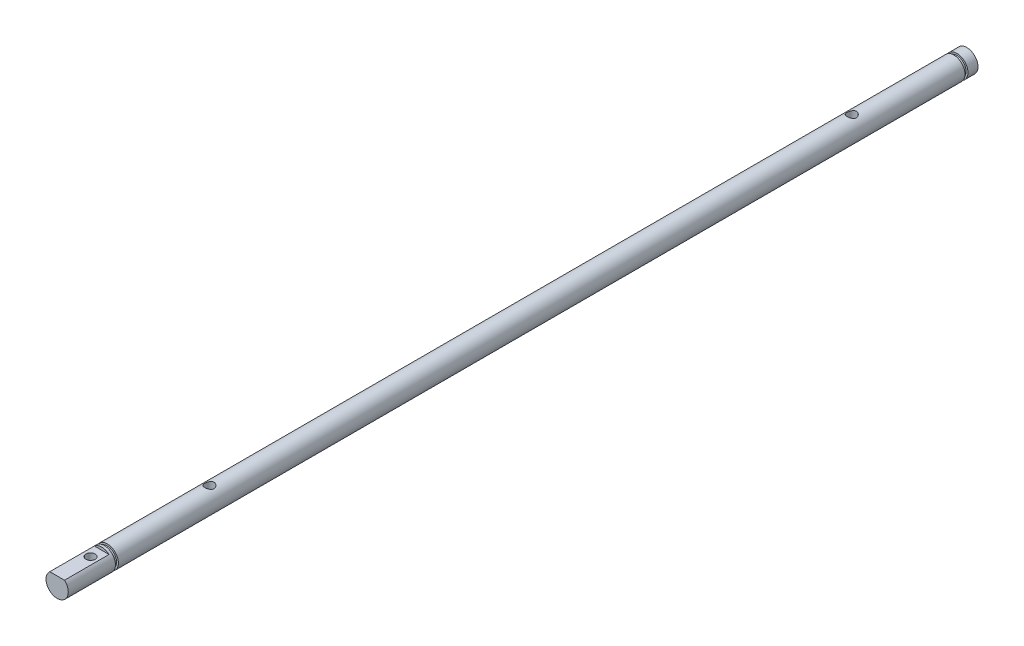
SolidWorks part; units mm, degrees
ref_plane "Front Plane" through (0, 0, 0) normal (0, 0, 1) x (1, 0, 0)
ref_plane "Top Plane" through (0, 0, 0) normal (0, 1, 0) x (1, 0, 0)
ref_plane "Right Plane" through (0, 0, 0) normal (1, 0, 0) x (0, 0, -1)
sketch "Sketch1" plane through (0, 0, 0) normal (0, 0, 1) x (1, 0, 0)
  circle A0 centre (0, 0) radius 3
  dimension "D1" = 6
extrude "Boss-Extrude1" add sketch "Sketch1" along normal blind 245
ref_axis "Axis1" through (0, 0, 245) along (0, 0, -1)
ref_plane "Plane2" through (0, 4, 0) normal (0, 1, 0) x (1, 0, 0)
sketch "Sketch21" plane through (0, 0, 245) normal (0, 0, 1) x (1, 0, 0)
  line L0 (-3, 0) -> (3, 0) construction
  line L1 (-1.9843, 2.25) -> (1.9843, 2.25)
  circle A0 centre (0, 0) radius 3 construction
  arc A2 (1.9843, 2.25) -> (-1.9843, 2.25) centre (0, 0) ccw
  dimension "D1" = 2.25
extrude "Cut-Extrude2" cut sketch "Sketch21" against normal blind 12
sketch "Sketch22" plane through (0, 2.25, 0) normal (0, 1, 0) x (1, 0, 0)
  line L7 (-1.9843, -245) -> (1.9843, -245)
  line L8 (1.9843, -245) -> (1.9843, -233)
  line L9 (1.9843, -233) -> (-1.9843, -233)
  line L10 (-1.9843, -233) -> (-1.9843, -245)
  line L11 (-1.9843, -245) -> (1.9843, -245) construction
  line L12 (1.9843, -245) -> (1.9843, -233) construction
  line L13 (1.9843, -233) -> (-1.9843, -233) construction
  line L14 (-1.9843, -233) -> (-1.9843, -245) construction
  circle A0 centre (0, -236) radius 1.5
  dimension "D5" = 3
  dimension "D2" = 3.9686
  dimension "D3" = 1.9843
  dimension "D4" = 9
  dimension "D1" = 0
hole_wizard "M3 Tapped Hole6" positions "3DSketch13" profile "Sketch23" tap size "M3" standard "ISO" end condition through all
sketch3d "3DSketch13"
  point P0 (0, 2.25, 236)
cosmetic thread "Hole Thread7" parameters "D2"=3
sketch "Sketch23" plane through (0, 2.25, 236) normal (1, 0, 0) x (0, 0, 1)
  line L0 (0, 0) -> (0, 5.25)
  line L1 (0, 5.25) -> (1.25, 5.25)
  line L2 (1.25, 5.25) -> (1.25, 0)
  line L5 (1.25, 0) -> (0, 0)
  line L11 (0, -6.35) -> (0, 107.95) construction
  dimension "Thru Tap Drill Dia." = 2.5
  dimension "Thru Tap Drill Depth" = 5.25
sketch "Sketch24" plane through (0, 0, 0) normal (1, 0, 0) x (0, 0, -1)
  line L0 (0, 3) -> (-233, 3) construction
  line L1 (-232.3, 3) -> (-231.5, 3)
  line L2 (-232.3, 3) -> (-232.3, 2.5)
  line L3 (-232.3, 2.5) -> (-231.5, 2.5)
  line L4 (-231.5, 3) -> (-231.5, 2.5)
  line L6 (0, -3) -> (0, 3) construction
  dimension "D1" = 0.8
  dimension "D2" = 0.5
  dimension "D3" = 231.5
ref_axis "Axis2" through (0, 0, 245) along (0, 0, -1)
revolve "Cut-Revolve1" cut sketch "Sketch24" angle 360 about axis through (0, 0, 245) along (0, 0, -1)
ref_plane "Plane3" through (0, 3.25, 0) normal (0, 1, 0) x (1, 0, 0)
sketch "Sketch26" plane through (0, 3.25, 0) normal (0, 1, 0) x (1, 0, 0)
  line L0 (-3, -245) -> (3, -245) construction
  line L1 (0, -31) -> (0, -204) construction
  line L2 (0, -204) -> (0, -231.5) construction
  line L3 (-2.5, -231.5) -> (2.5, -231.5) construction
  circle A0 centre (0, -204) radius 1.5
  circle A1 centre (0, -31) radius 1.5
  dimension "D1" = 173
  dimension "D2" = 3
  dimension "D3" = 41
hole_wizard "M3 Tapped Hole7" positions "3DSketch14" profile "Sketch27" tap size "M3" standard "ISO" end condition through all
sketch3d "3DSketch14"
  point P0 (0, 3.25, 204)
  point P3 (0, 3.25, 31)
sketch "Sketch27" plane through (0, 3.25, 204) normal (1, 0, 0) x (0, 0, 1)
  line L0 (0, 0) -> (0, 6.25)
  line L1 (0, 6.25) -> (1.25, 6.25)
  line L2 (1.25, 6.25) -> (1.25, 0)
  line L5 (1.25, 0) -> (0, 0)
  line L11 (0, -6.35) -> (0, 107.95) construction
  dimension "Thru Tap Drill Dia." = 2.5
  dimension "Thru Tap Drill Depth" = 6.25
sketch "Sketch28" plane through (0, 0, 0) normal (0, 1, 0) x (1, 0, 0)
  line L0 (3, -231.5) -> (3, 0) construction
  line L1 (3, -2.7) -> (2.5, -2.7)
  line L2 (3, -2.7) -> (3, -3.5)
  line L3 (3, -3.5) -> (2.5, -3.5)
  line L4 (2.5, -2.7) -> (2.5, -3.5)
  line L6 (3, 0) -> (-3, 0) construction
  dimension "D1" = 0.8
  dimension "D2" = 0.5
  dimension "D3" = 3.5
revolve "Cut-Revolve2" cut sketch "Sketch28" angle 360 about axis through (0, 0, 245) along (0, 0, -1)
equation "\"D3@Sketch22\"=\"D2@Sketch22\"/2"
